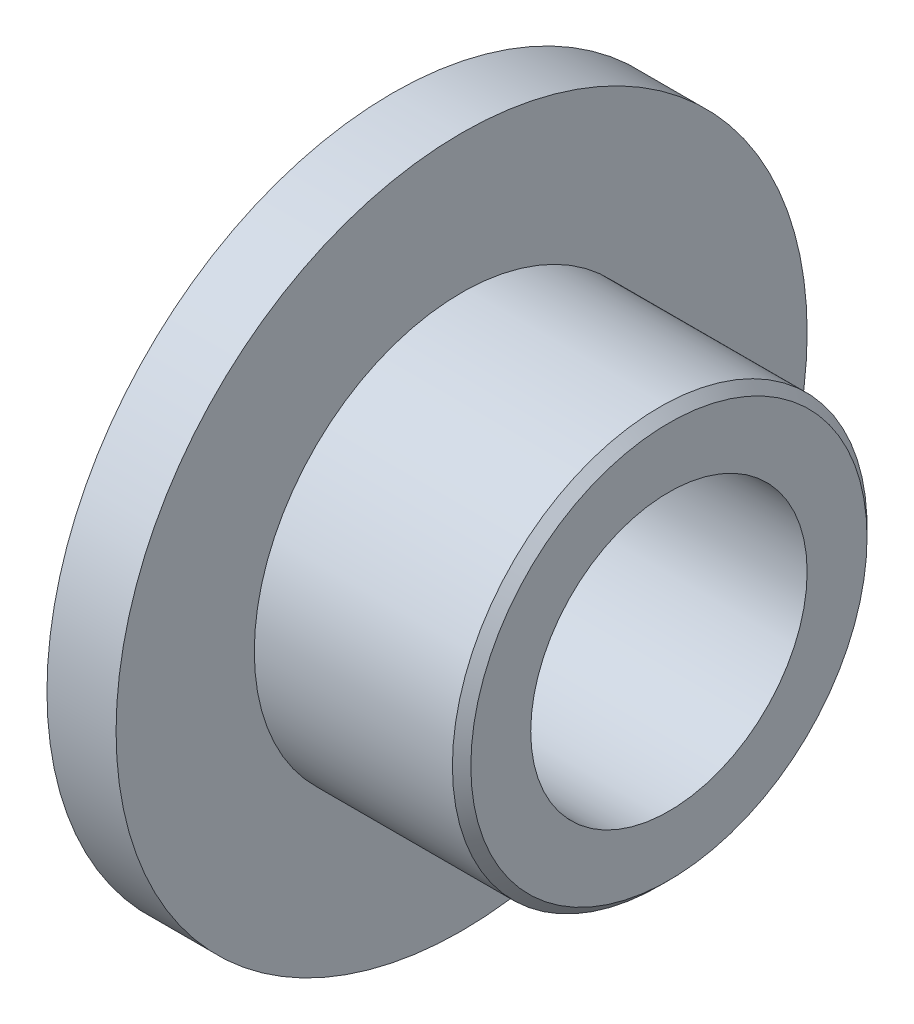
SolidWorks part; units mm, degrees
ref_plane "前视基准面" through (0, 0, 0) normal (0, 0, 1) x (1, 0, 0)
ref_plane "上视基准面" through (0, 0, 0) normal (0, 1, 0) x (1, 0, 0)
ref_plane "右视基准面" through (0, 0, 0) normal (1, 0, 0) x (0, 0, -1)
ref_plane "基准面1" through (0, 0, 0) normal (0, 0, -1) x (-1, 0, 0)
sketch "草图1" plane through (0, 0, 0) normal (0, 0, -1) x (-1, 0, 0)
  line L0 (0, 3.75) -> (-0.75, 3.75)
  line L1 (-0.75, 3.75) -> (-0.75, 2.25)
  line L2 (-0.75, 2.25) -> (-2.9, 2.25)
  line L3 (-2.9, 2.25) -> (-3, 2.15)
  line L4 (-3, 2.15) -> (-3, 1.5)
  line L5 (-3, 1.5) -> (0, 1.5)
  line L6 (0, 1.5) -> (0, 3.75)
  line L7 (-4, 0) -> (0, 0) construction
  dimension "D1" = 4.5
  dimension "D2" = 3
  dimension "D3" = 0.75
  dimension "D4" = 2.25
  dimension "D5" = 0.1414
  dimension "D6" = 45
  dimension "D7" = 3
  dimension "D8" = 7.5
revolve "旋转1" add sketch "草图1" angle 360 about L7
